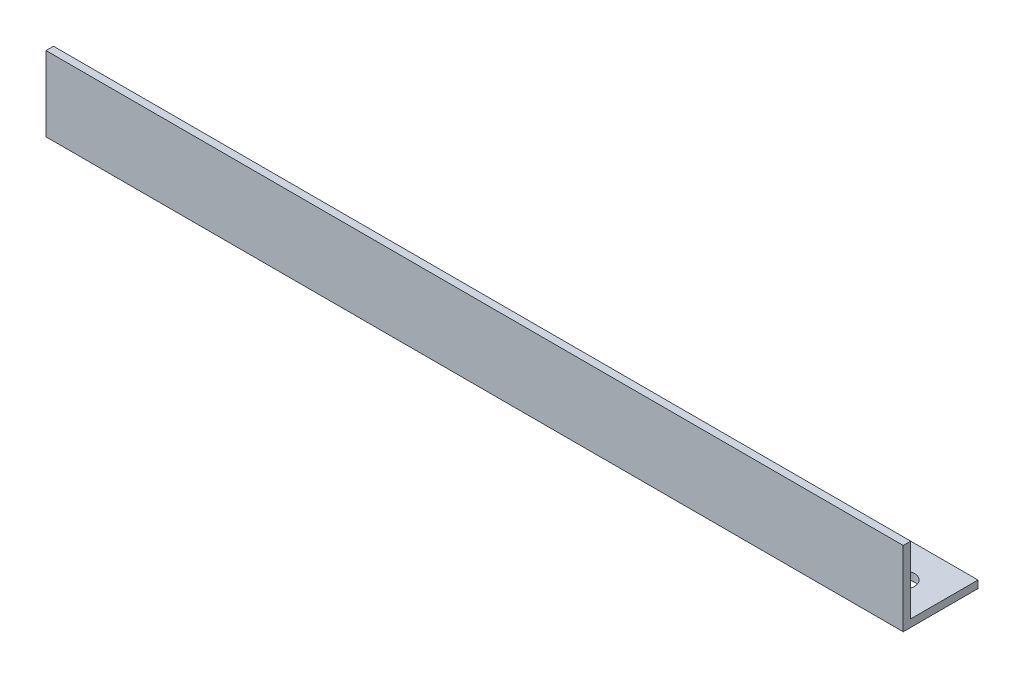
SolidWorks part; units mm, degrees
ref_plane "Спереди" through (0, 0, 0) normal (0, 0, 1) x (1, 0, 0)
ref_plane "Сверху" through (0, 0, 0) normal (0, 1, 0) x (1, 0, 0)
ref_plane "Справа" through (0, 0, 0) normal (1, 0, 0) x (0, 0, -1)
sketch "Эскиз1" plane through (0, 0, 0) normal (1, 0, 0) x (0, 0, -1)
  line L0 (0, 0) -> (0, 15)
  line L1 (0, 15) -> (1.5, 15)
  line L2 (1.5, 15) -> (1.5, 1.5)
  line L3 (1.5, 1.5) -> (15, 1.5)
  line L4 (15, 1.5) -> (15, 0)
  line L5 (15, 0) -> (0, 0)
  dimension "D1" = 15
  dimension "D2" = 15
  dimension "D3" = 1.5
  dimension "D4" = 1.5
extrude "Бобышка-Вытянуть1" add sketch "Эскиз1" along normal blind 172
sketch "Эскиз2" plane through (0, 0, 0) normal (0, -1, 0) x (1, 0, 0)
  line L0 (0, 0) -> (0, -15) construction
  line L1 (172, 0) -> (172, -15) construction
  circle A0 centre (7.5, -7.5) radius 2.25
  circle A1 centre (164.5, -7.5) radius 2.25
  dimension "D1" = 4.5
  dimension "D2" = 7.5
  dimension "D3" = 4.5
  dimension "D4" = 7.5
extrude "Вырез-Вытянуть1" cut sketch "Эскиз2" against normal through all
